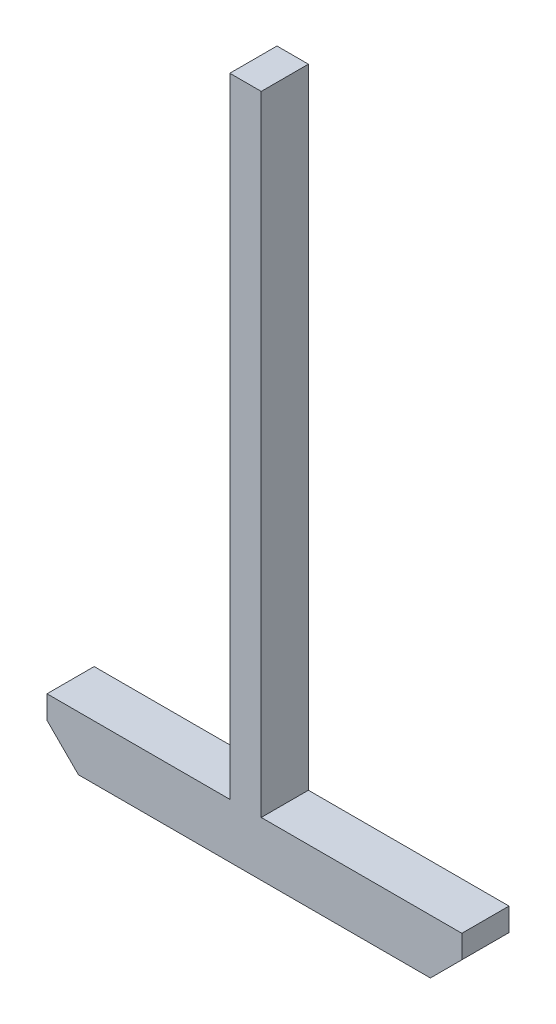
SolidWorks part; units mm, degrees
ref_plane "Front Plane" through (0, 0, 0) normal (0, 0, 1) x (1, 0, 0)
ref_plane "Top Plane" through (0, 0, 0) normal (0, 1, 0) x (1, 0, 0)
ref_plane "Right Plane" through (0, 0, 0) normal (1, 0, 0) x (0, 0, -1)
sketch "Sketch1" plane through (0, 0, 0) normal (0, 0, 1) x (1, 0, 0)
  line L1 (5.5138, 96.117) -> (5.5138, 146.117)
  line L2 (-4.4862, 146.117) -> (-4.4862, 96.117)
  line L3 (-52.6321, -71.2012) -> (59.3155, -71.2012)
  line L5 (-62.6321, -61.2012) -> (-52.6321, -71.2012)
  line L6 (59.3155, -71.2012) -> (69.3155, -61.2012)
  line L11 (-62.6321, -53.883) -> (-62.6321, -61.2012)
  line L12 (-62.6321, -53.883) -> (-4.4862, -53.883)
  line L13 (-4.4862, 96.117) -> (-4.4862, -53.883)
  line L14 (-4.4862, 146.117) -> (5.5138, 146.117)
  line L15 (5.5138, 96.117) -> (5.5138, -53.883)
  line L16 (5.5138, -53.883) -> (69.3155, -53.883)
  line L17 (69.3155, -53.883) -> (69.3155, -61.2012)
extrude "Boss-Extrude1" add sketch "Sketch1" along normal blind 15
